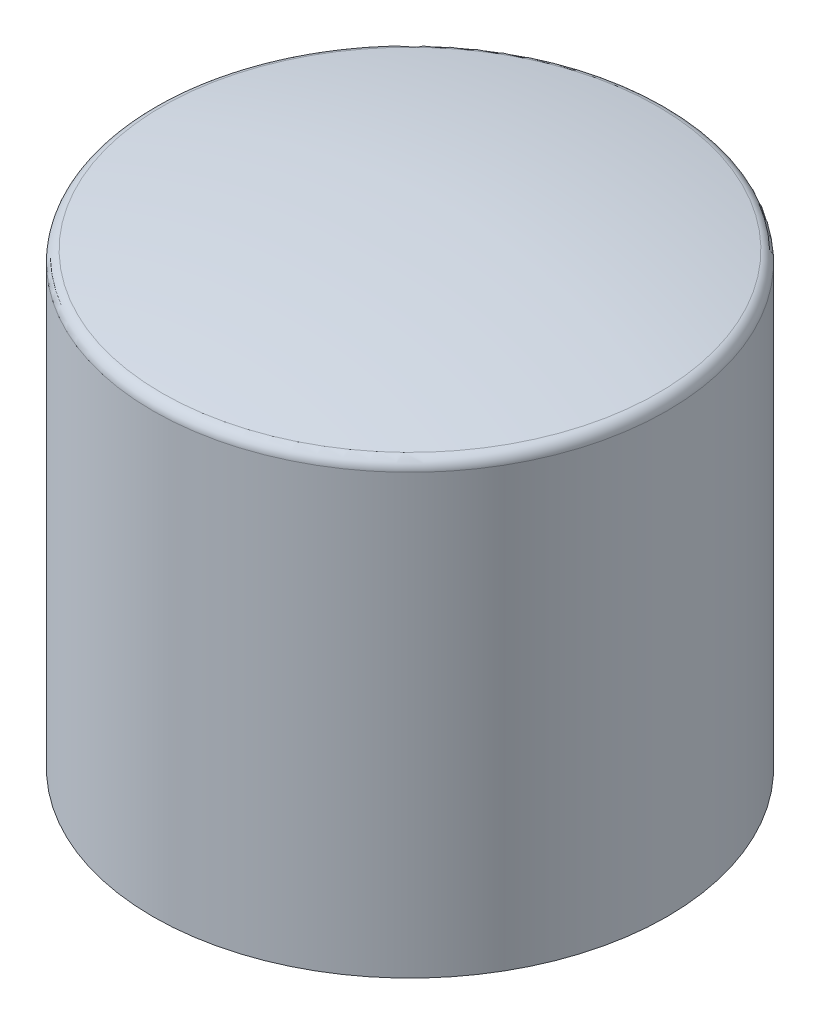
SolidWorks part; units mm, degrees
ref_plane "Front Plane" through (0, 0, 0) normal (0, 0, 1) x (1, 0, 0)
ref_plane "Top Plane" through (0, 0, 0) normal (0, 1, 0) x (1, 0, 0)
ref_plane "Right Plane" through (0, 0, 0) normal (1, 0, 0) x (0, 0, -1)
sketch "Sketch2" plane through (0, 0, 0) normal (1, 0, 0) x (0, 0, -1)
  line L0 (11.5, -1.1698) -> (11.5, -21.1698)
  line L1 (11.5, -21.1698) -> (0, -21.1698)
  line L2 (0, -21.1698) -> (0, 0)
  spline S0 degree 2 poles (0, 0) (5.8092, 0.0241) (11.5, -1.1698) knots 0 0 0 1 1 1
  dimension "D1" = 20
  dimension "D2" = 11.5
revolve "Revolve1" add sketch "Sketch2" angle 360 about L2
fillet "Fillet1" radius 0.5 1 edges at (0, -1.1698, -11.5)
